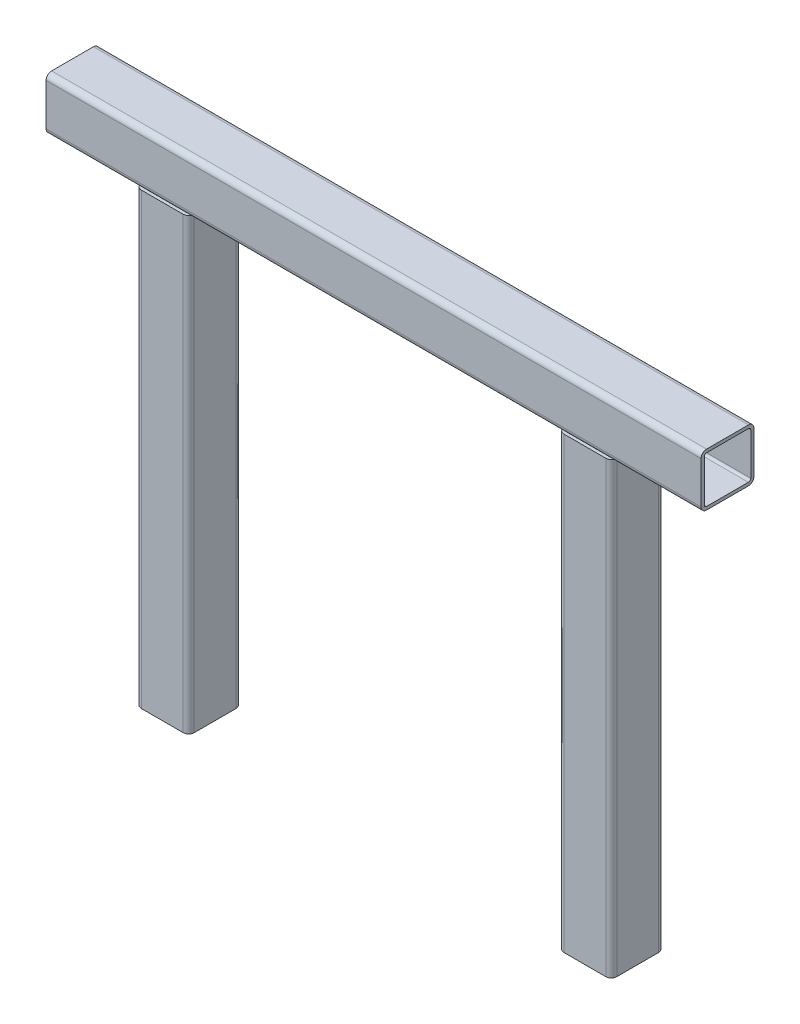
SolidWorks part; units mm, degrees
ref_plane "前视基准面" through (0, 0, 0) normal (0, 0, 1) x (1, 0, 0)
ref_plane "上视基准面" through (0, 0, 0) normal (0, 1, 0) x (1, 0, 0)
ref_plane "右视基准面" through (0, 0, 0) normal (1, 0, 0) x (0, 0, -1)
sketch "草图1" plane through (0, 0, 0) normal (0, 0, 1) x (1, 0, 0)
  line L0 (-643.271, 0) -> (542.4598, 0) construction
  line L1 (0, 540.0596) -> (0, -765.6845) construction
  line L2 (-310, 0) -> (310, 0)
  line L3 (-200, 0) -> (-200, -450)
  line L4 (200, 0) -> (200, -450)
  point P11 (0, 0)
  dimension "D1" = 400
  dimension "D2" = 110
  dimension "D3" = 450
  dimension "D4" = 0
other "50x50xt2 50 X 30 X 2.6(1)"
ref_plane "基准面1" through (-310, 0, 0) normal (1, 0, 0) x (0, 1, 0)
sketch "Sketch17" plane through (-310, 0, 0) normal (1, 0, 0) x (0, 1, 0)
  line L0 (-19.8, -22) -> (19.8, -22)
  line L1 (-22, -19.8) -> (-22, 19.8)
  line L2 (19.8, 22) -> (-19.8, 22)
  line L3 (22, 19.8) -> (22, -19.8)
  line L4 (-19.8, -25) -> (19.8, -25)
  line L5 (-25, -19.8) -> (-25, 19.8)
  line L6 (19.8, 25) -> (-19.8, 25)
  line L7 (25, 19.8) -> (25, -19.8)
  arc A0 (25, 19.8) -> (19.8, 25) centre (19.8, 19.8) ccw
  arc A1 (19.8, -25) -> (25, -19.8) centre (19.8, -19.8) ccw
  arc A2 (-25, -19.8) -> (-19.8, -25) centre (-19.8, -19.8) ccw
  arc A3 (-19.8, 25) -> (-25, 19.8) centre (-19.8, 19.8) ccw
  arc A4 (-19.8, 22) -> (-22, 19.8) centre (-19.8, 19.8) ccw
  arc A5 (22, 19.8) -> (19.8, 22) centre (19.8, 19.8) ccw
  arc A6 (19.8, -22) -> (22, -19.8) centre (19.8, -19.8) ccw
  arc A7 (-22, -19.8) -> (-19.8, -22) centre (-19.8, -19.8) ccw
  point P0 (0, 25)
  point P1 (25, 0)
  point P2 (0, -25)
  point P3 (-25, 0)
  point P4 (-25, 25)
  point P5 (25, 25)
  point P6 (25, -25)
  point P7 (-25, -25)
  point P8 (0, 0)
  point P33 (0, 0)
  dimension "D1" = 5.2
  dimension "Thickness" = 3
  dimension "V_leg" = 50
  dimension "H_leg" = 50
